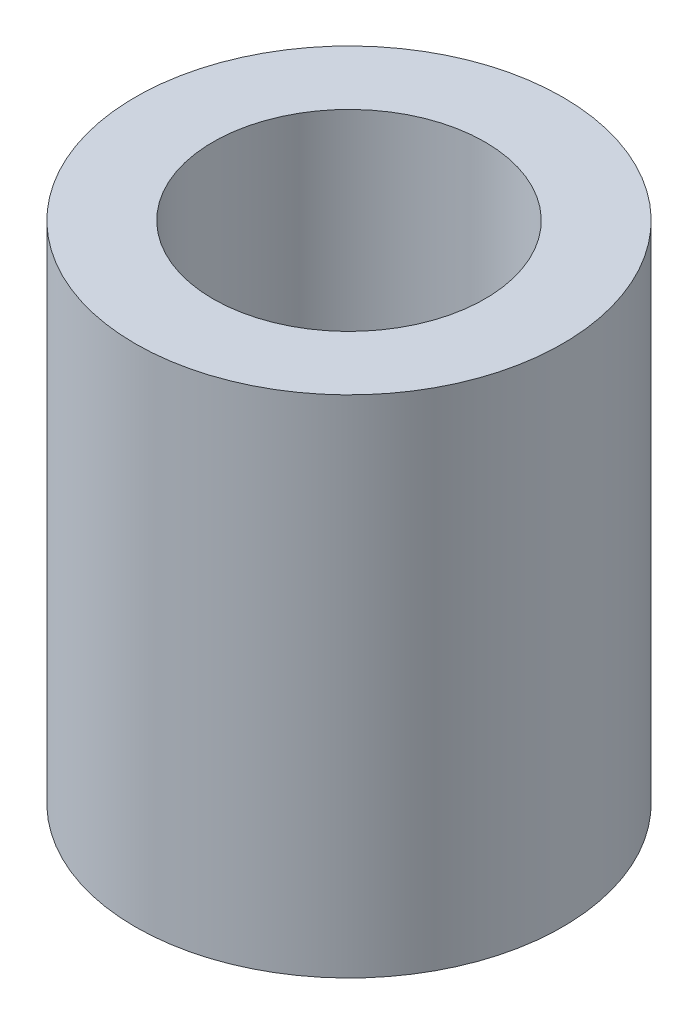
SolidWorks part; units mm, degrees
ref_plane "Front Plane" through (0, 0, 0) normal (0, 0, 1) x (1, 0, 0)
ref_plane "Top Plane" through (0, 0, 0) normal (0, 1, 0) x (1, 0, 0)
ref_plane "Right Plane" through (0, 0, 0) normal (1, 0, 0) x (0, 0, -1)
sketch "Sketch1" plane through (0, 0, 0) normal (0, 1, 0) x (1, 0, 0)
  circle A0 centre (0, 0) radius 2.75
  circle A1 centre (0, 0) radius 1.75
  dimension "D1" = 5.5
  dimension "D2" = 3.5
extrude "Boss-Extrude1" add sketch "Sketch1" along normal blind 6.5
